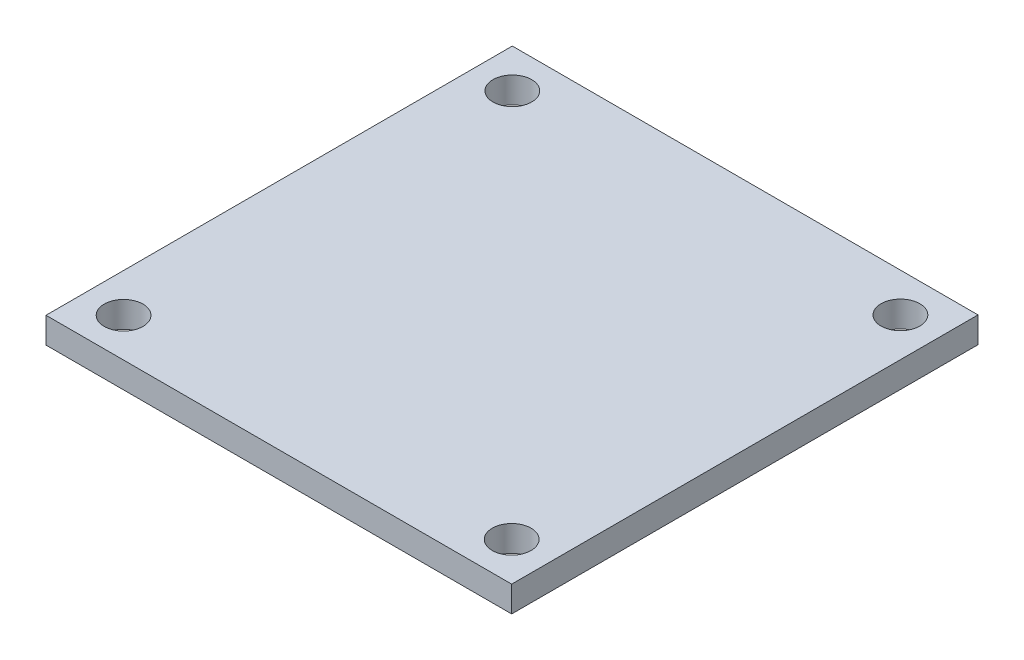
SolidWorks part; units mm, degrees
ref_plane "Front Plane" through (0, 0, 0) normal (0, 0, 1) x (1, 0, 0)
ref_plane "Top Plane" through (0, 0, 0) normal (0, 1, 0) x (1, 0, 0)
ref_plane "Right Plane" through (0, 0, 0) normal (1, 0, 0) x (0, 0, -1)
sketch "Sketch1" plane through (0, 0, 0) normal (0, 1, 0) x (1, 0, 0)
  line L0 (0, 0) -> (-13.7039, 0) construction
  line L1 (-18.0086, -18.034) -> (18.0086, -18.034)
  line L2 (-18.0086, -18.034) -> (-18.0086, 18.034)
  line L3 (-18.0086, 18.034) -> (18.0086, 18.034)
  line L4 (18.0086, -18.034) -> (18.0086, 18.034)
  line L5 (-18.0086, -18.034) -> (18.0086, 18.034) construction
  line L6 (-18.0086, 18.034) -> (18.0086, -18.034) construction
  line L7 (0, 0) -> (0, 10.9277) construction
  circle A0 centre (-15.0086, 15.034) radius 1.5
  circle A1 centre (15.0086, 15.034) radius 1.5
  circle A2 centre (-15.0086, -15.034) radius 1.5
  circle A3 centre (15.0086, -15.034) radius 1.5
  point P0 (0, 0)
  dimension "D5" = 3
  dimension "D1" = 36.0172
  dimension "D2" = 36.068
  dimension "D3" = 3
  dimension "D4" = 3
extrude "Boss-Extrude1" add sketch "Sketch1" along normal blind 2
